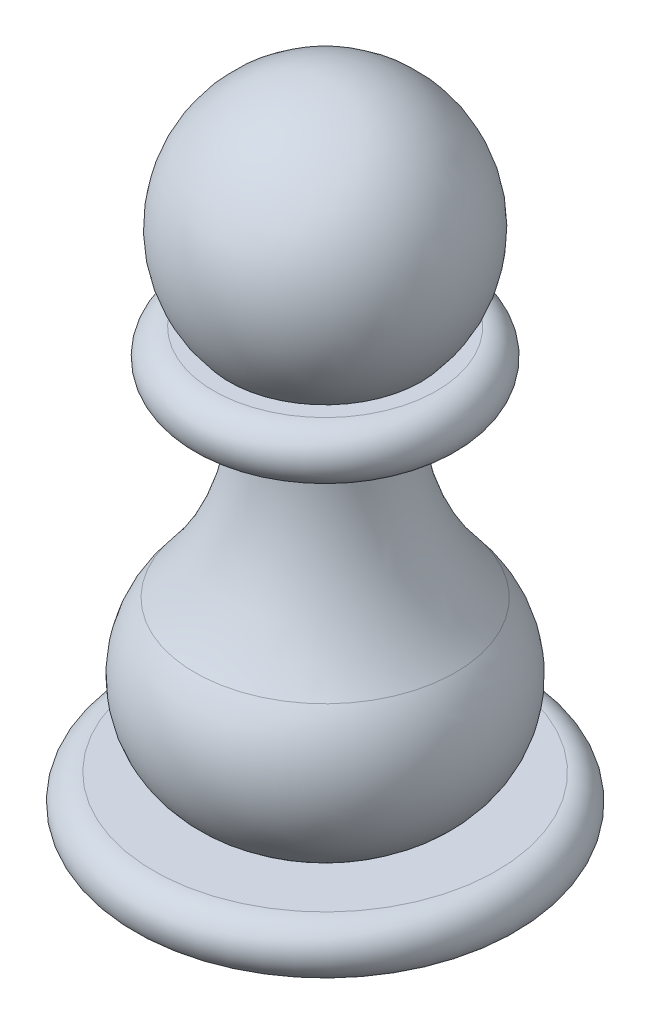
SolidWorks part; units mm, degrees
ref_plane "Front Plane" through (0, 0, 0) normal (0, 0, 1) x (1, 0, 0)
ref_plane "Top Plane" through (0, 0, 0) normal (0, 1, 0) x (1, 0, 0)
ref_plane "Right Plane" through (0, 0, 0) normal (1, 0, 0) x (0, 0, -1)
sketch "Sketch1" plane through (0, 0, 0) normal (0, 0, 1) x (1, 0, 0)
  line L0 (0, 0) -> (0, 38) construction
  line L1 (0, 25.5) -> (-6.5, 25.5)
  line L2 (-6.5, 22.5) -> (0, 22.5)
  line L3 (0, 0) -> (-10, 0)
  line L4 (-10, 3) -> (0, 3)
  arc A0 (0, 38) -> (-5.5902, 25.5) centre (0, 30.5) ccw
  arc A1 (-6.5, 25.5) -> (-6.5, 22.5) centre (-6.5, 24) ccw
  arc A2 (-10, 0) -> (-10, 3) centre (-10, 1.5) cw
  arc A3 (-7.5963, 11.8166) -> (-4, 22.5) centre (-18.9726, 21.5932) ccw
  arc A4 (-7.5963, 11.8166) -> (-6.5, 3) centre (-3.0459, 7.906) ccw
  point P19 (0, 0)
  point P20 (0, 24.3018)
  point P21 (0, 0)
  point P22 (-9, 7.1656)
  point P23 (-8, 24)
  point P24 (-6.5, 3)
  point P25 (0, 0)
  point P26 (-11.5, 1.5)
  dimension "D3" = 6
  dimension "D4" = 15
  dimension "D6" = 8
  dimension "D7" = 7.5
  dimension "D8" = 6.5
  dimension "D11" = 9
  dimension "D12" = 12.5
  dimension "D2" = 3
  dimension "D5" = 38
  dimension "D9" = 3
  dimension "D10" = 4
  dimension "D13" = 11.5
revolve "Revolve2" add sketch "Sketch1" angle 360 about L0
